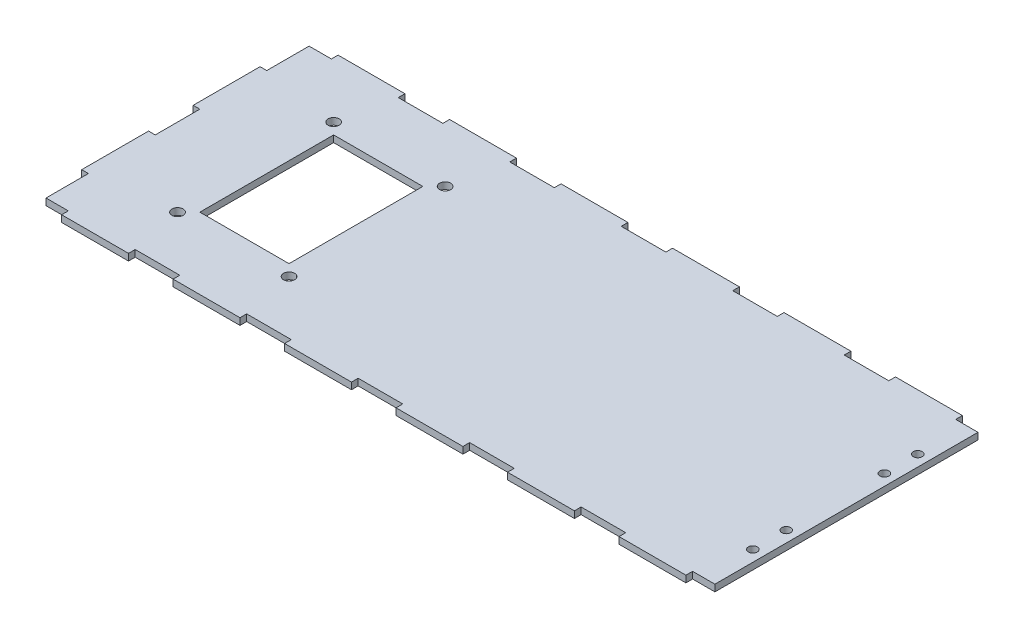
SolidWorks part; units mm, degrees
ref_plane "前视基准面" through (0, 0, 0) normal (0, 0, 1) x (1, 0, 0)
ref_plane "上视基准面" through (0, 0, 0) normal (0, 1, 0) x (1, 0, 0)
ref_plane "右视基准面" through (0, 0, 0) normal (1, 0, 0) x (0, 0, -1)
sketch "草图4" plane through (0, 0, 0) normal (0, 1, 0) x (1, 0, 0)
  line L0 (10, 0) -> (0, 0)
  line L1 (0, 0) -> (0, -19)
  line L2 (0, -19) -> (-3, -19)
  line L3 (-3, -19) -> (-3, -49)
  line L4 (-3, -49) -> (0, -49)
  line L5 (0, -49) -> (0, -69)
  line L6 (0, -69) -> (-3, -69)
  line L7 (-3, -69) -> (-3, -99)
  line L8 (-3, -99) -> (0, -99)
  line L9 (0, -118) -> (10, -118)
  line L10 (10, -118) -> (10, -121)
  line L11 (10, -121) -> (40, -121)
  line L12 (40, -121) -> (40, -118)
  line L13 (40, -118) -> (60, -118)
  line L14 (60, -118) -> (60, -121)
  line L15 (60, -121) -> (90, -121)
  line L16 (90, -121) -> (90, -118)
  line L17 (90, -118) -> (110, -118)
  line L18 (110, -118) -> (110, -121)
  line L19 (110, -121) -> (140, -121)
  line L20 (140, -121) -> (140, -118)
  line L21 (140, -118) -> (160, -118)
  line L22 (160, -118) -> (160, -121)
  line L23 (300, 0) -> (300, -118)
  line L24 (160, -121) -> (190, -121)
  line L25 (190, -121) -> (190, -118)
  line L26 (190, -118) -> (210, -118)
  line L27 (210, -118) -> (210, -121)
  line L28 (210, -121) -> (240, -121)
  line L29 (240, -121) -> (240, -118)
  line L30 (240, -118) -> (260, -118)
  line L31 (260, -118) -> (260, -121)
  line L32 (260, -121) -> (290, -121)
  line L33 (290, -121) -> (290, -118)
  line L34 (290, -118) -> (300, -118)
  line L44 (300, 0) -> (290, 0)
  line L45 (290, 0) -> (290, 3)
  line L46 (290, 3) -> (260, 3)
  line L47 (260, 3) -> (260, 0)
  line L48 (260, 0) -> (240, 0)
  line L49 (240, 0) -> (240, 3)
  line L50 (240, 3) -> (210, 3)
  line L51 (210, 3) -> (210, 0)
  line L52 (210, 0) -> (190, 0)
  line L53 (190, 0) -> (190, 3)
  line L54 (190, 3) -> (160, 3)
  line L55 (160, 3) -> (160, 0)
  line L56 (160, 0) -> (140, 0)
  line L57 (140, 0) -> (140, 3)
  line L58 (140, 3) -> (110, 3)
  line L59 (110, 3) -> (110, 0)
  line L60 (110, 0) -> (90, 0)
  line L61 (90, 0) -> (90, 3)
  line L62 (90, 3) -> (60, 3)
  line L63 (60, 3) -> (60, 0)
  line L64 (60, 0) -> (40, 0)
  line L65 (40, 0) -> (40, 3)
  line L66 (40, 3) -> (10, 3)
  line L67 (0, -99) -> (0, -118)
  line L68 (10, 3) -> (10, 0)
extrude "凸台-拉伸1" add sketch "草图4" against normal blind 3
sketch "草图5" plane through (0, 0, 0) normal (0, 1, 0) x (1, 0, 0)
  line L0 (300, -29.5) -> (300, -88.5) construction
  line L1 (300, 0) -> (300, -118) construction
  line L2 (300, -81) -> (300, -96) construction
  line L3 (300, -96) -> (295, -96) construction
  line L4 (0, -59) -> (40, -59) construction
  line L5 (40, -29) -> (80, -29)
  line L6 (40, -29) -> (40, -89)
  line L7 (40, -89) -> (80, -89)
  line L8 (80, -29) -> (80, -89)
  line L9 (0, -49) -> (0, -69) construction
  line L10 (40, -29) -> (30, -19) construction
  line L11 (60, -89) -> (60, -29) construction
  line L12 (30, -19) -> (90, -19) construction
  line L13 (30, -19) -> (30, -99) construction
  line L14 (30, -99) -> (90, -99) construction
  line L15 (90, -19) -> (90, -99) construction
  line L16 (30, -19) -> (90, -99) construction
  line L17 (30, -99) -> (90, -19) construction
  circle A0 centre (295, -96) radius 2
  circle A1 centre (295, -81) radius 2
  circle A2 centre (295, -22) radius 2
  circle A3 centre (295, -37) radius 2
  circle A4 centre (35, -24) radius 2.5
  circle A5 centre (35, -94) radius 2.5
  circle A6 centre (85, -94) radius 2.5
  circle A7 centre (85, -24) radius 2.5
  point P7 (300, -59)
  point P10 (300, -88.5)
  point P31 (60, -59)
extrude "切除-拉伸1" cut sketch "草图5" against normal blind 3
